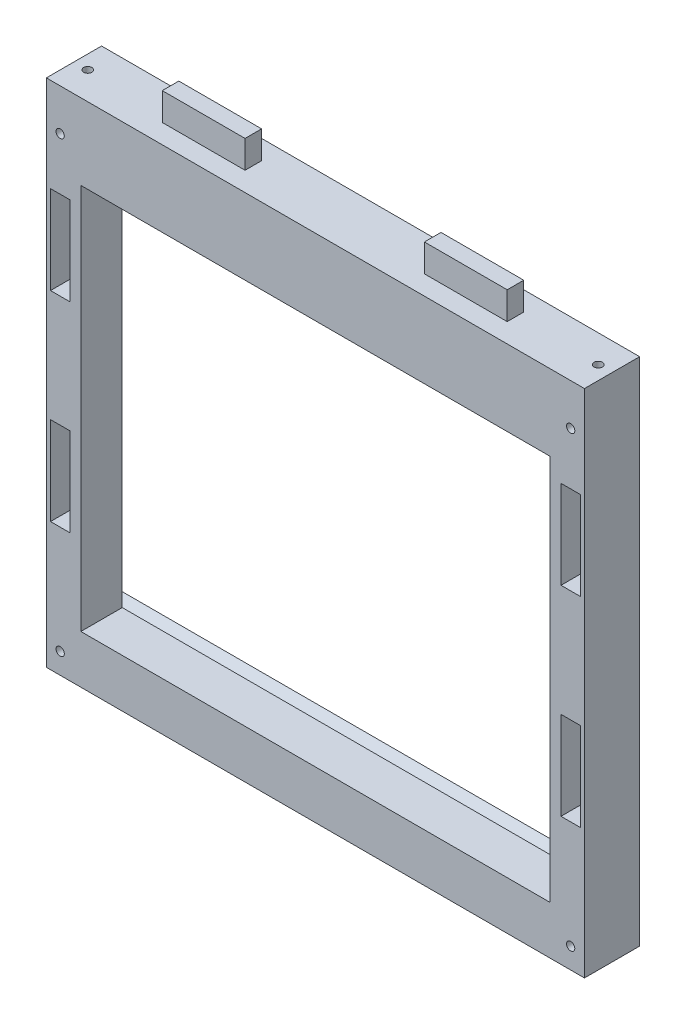
SolidWorks part; units mm, degrees
material "ABS"
ref_plane "Plano frontal" through (0, 0, 0) normal (0, 0, 1) x (1, 0, 0)
ref_plane "Plano superior" through (0, 0, 0) normal (0, 1, 0) x (1, 0, 0)
ref_plane "Plano direito" through (0, 0, 0) normal (1, 0, 0) x (0, 0, -1)
sketch "Esboço1" plane through (0, 0, 0) normal (0, 0, 1) x (1, 0, 0)
  line L1 (97.5, -92.5) -> (-97.5, -92.5)
  line L2 (97.5, -92.5) -> (97.5, 92.5)
  line L3 (97.5, 92.5) -> (-97.5, 92.5)
  line L4 (-97.5, -92.5) -> (-97.5, 92.5)
  line L5 (97.5, -92.5) -> (-97.5, 92.5) construction
  line L6 (97.5, 92.5) -> (-97.5, -92.5) construction
  point P0 (0, 0)
  dimension "D1" = 185
  dimension "D2" = 195
extrude "Ressalto-extrusão1" add sketch "Esboço1" along normal blind 20
sketch "Esboço3" plane through (0, 0, 20) normal (0, 0, 1) x (1, 0, 0)
  line L0 (-135.0581, -80) -> (163.4742, -80) construction
  line L6 (-97.5, 92.5) -> (-97.5, -92.5) construction
  line L7 (-89, -46) -> (-96, -46)
  line L8 (97.5, 92.5) -> (-97.5, 92.5) construction
  line L9 (-89, -46) -> (-89, -14)
  line L10 (-89, -14) -> (-96, -14)
  line L15 (0, 106.7871) -> (0, -117.3693) construction
  line L16 (-96, -46) -> (-96, -14)
  line L17 (-89, -46) -> (-96, -14) construction
  line L22 (-89, -14) -> (-96, -46) construction
  line L23 (89, -14) -> (96, -46) construction
  line L28 (-121.8027, 6.25) -> (143.8497, 6.25) construction
  line L29 (89, -46) -> (96, -14) construction
  line L30 (96, -46) -> (96, -14)
  line L31 (89, -14) -> (96, -14)
  line L32 (89, -46) -> (89, -14)
  line L33 (89, -46) -> (96, -46)
  line L34 (89, 58.5) -> (96, 26.5) construction
  line L35 (89, 26.5) -> (96, 58.5) construction
  line L36 (89, 58.5) -> (96, 58.5)
  line L37 (89, 58.5) -> (89, 26.5)
  line L38 (89, 26.5) -> (96, 26.5)
  line L39 (96, 58.5) -> (96, 26.5)
  line L40 (-89, 26.5) -> (-96, 58.5) construction
  line L41 (-89, 58.5) -> (-96, 26.5) construction
  line L42 (-96, 58.5) -> (-96, 26.5)
  line L43 (-89, 26.5) -> (-96, 26.5)
  line L44 (-89, 58.5) -> (-89, 26.5)
  line L45 (-89, 58.5) -> (-96, 58.5)
  point P2 (-92.5, -30)
  point P16 (92.5, -30)
  point P23 (92.5, 42.5)
  point P28 (-92.5, 42.5)
  dimension "D1" = 7
  dimension "D2" = 1.5
  dimension "D3" = 32
  dimension "D4" = 172.5
  dimension "D5" = 86.25
  dimension "D6" = 50
extrude "Corte-extrusão1" cut sketch "Esboço3" against normal blind 10
sketch "Esboço6" plane through (0, 0, 0) normal (0, 0, -1) x (-1, 0, 0)
  line L0 (0, 110.3211) -> (0, -118.4678) construction
  line L1 (-131.3107, -6.25) -> (134.1127, -6.25) construction
  line L2 (97.5, -92.5) -> (-97.5, -92.5) construction
  line L3 (-97.5, -92.5) -> (-97.5, 92.5) construction
  line L4 (-97.5, 92.5) -> (97.5, 92.5) construction
  circle A0 centre (-92.5, 77.5) radius 1.5
  circle A1 centre (92.5, 77.5) radius 1.5
  circle A2 centre (-92.5, -85) radius 1.5
  circle A3 centre (92.5, -85) radius 1.5
  dimension "D2" = 3
  dimension "D3" = 5
  dimension "D4" = 15
  dimension "D5" = 3
  dimension "D1" = 86.25
  dimension "D6" = 5
  dimension "D7" = 7.5
extrude "Corte-extrusão4" cut sketch "Esboço6" against normal through all
sketch "Esboço8" plane through (0, 0, 0) normal (0, 0, -1) x (-1, 0, 0)
  line L0 (0, 100.342) -> (0, -100.3526) construction
  line L1 (-125.2567, -5) -> (132.6442, -5) construction
  line L3 (-97.5, 92.5) -> (97.5, 92.5) construction
  line L4 (85, -75) -> (-85, -75)
  line L5 (85, -75) -> (85, 65)
  line L6 (85, 65) -> (-85, 65)
  line L7 (-85, -75) -> (-85, 65)
  line L8 (85, -75) -> (-85, 65) construction
  line L9 (85, 65) -> (-85, -75) construction
  point P7 (0, -5)
  dimension "D1" = 97.5
  dimension "D2" = 140
  dimension "D3" = 170
extrude "Corte-extrusão6" cut sketch "Esboço8" against normal through all
sketch "Esboço9" plane through (-97.5, 0, 0) normal (-1, 0, 0) x (0, 0, 1)
  line L0 (-27.5071, -5) -> (51.1391, -5) construction
  line L2 (0, -75) -> (0, 65)
  line L3 (0, 92.5) -> (0, -92.5) construction
  line L4 (0, 65) -> (5, 68.501)
  line L5 (5, 68.501) -> (5, -78.501)
  line L6 (0, -75) -> (5, -78.501)
  line L7 (20, 92.5) -> (0, 92.5) construction
  point P13 (5, -5)
  point P14 (0, -5)
  dimension "D1" = 97.5
  dimension "D2" = 70
  dimension "D3" = 55
  dimension "D4" = 5
extrude "Corte-extrusão7" cut sketch "Esboço9" against normal blind 190
sketch "Esboço10" plane through (0, 92.5, 0) normal (0, 1, 0) x (1, 0, 0)
  line L0 (-140.1165, -10) -> (144, -10) construction
  line L1 (97.5, 0) -> (-97.5, 0) construction
  line L2 (0, 17.1601) -> (0, -31.2111) construction
  line L3 (-97.5, -20) -> (-97.5, 0) construction
  line L4 (-32.5, -13) -> (-62.5, -13)
  line L5 (-32.5, -13) -> (-32.5, -7)
  line L6 (-32.5, -7) -> (-62.5, -7)
  line L7 (-62.5, -13) -> (-62.5, -7)
  line L8 (-32.5, -13) -> (-62.5, -7) construction
  line L9 (-32.5, -7) -> (-62.5, -13) construction
  line L10 (32.5, -7) -> (62.5, -13) construction
  line L11 (32.5, -13) -> (62.5, -7) construction
  line L12 (62.5, -13) -> (62.5, -7)
  line L13 (32.5, -7) -> (62.5, -7)
  line L14 (32.5, -13) -> (32.5, -7)
  line L15 (32.5, -13) -> (62.5, -13)
  point P6 (-47.5, -10)
  point P20 (47.5, -10)
  dimension "D1" = 10
  dimension "D2" = 30
  dimension "D3" = 6
  dimension "D4" = 50
extrude "Ressalto-extrusão2" add sketch "Esboço10" along normal blind 10
sketch "Esboço11" plane through (0, 92.5, 0) normal (0, 1, 0) x (1, 0, 0)
  line L0 (-121.8181, -10) -> (119.7392, -10) construction
  line L1 (97.5, -20) -> (-97.5, -20) construction
  line L2 (-97.5, -20) -> (-97.5, 0) construction
  line L3 (0, 10.5459) -> (0, -34.3916) construction
  circle A0 centre (-92.5, -10) radius 1.5
  circle A1 centre (92.5, -10) radius 1.5
  dimension "D2" = 3
  dimension "D3" = 5
  dimension "D1" = 10
extrude "Corte-extrusão8" cut sketch "Esboço11" against normal blind 8
